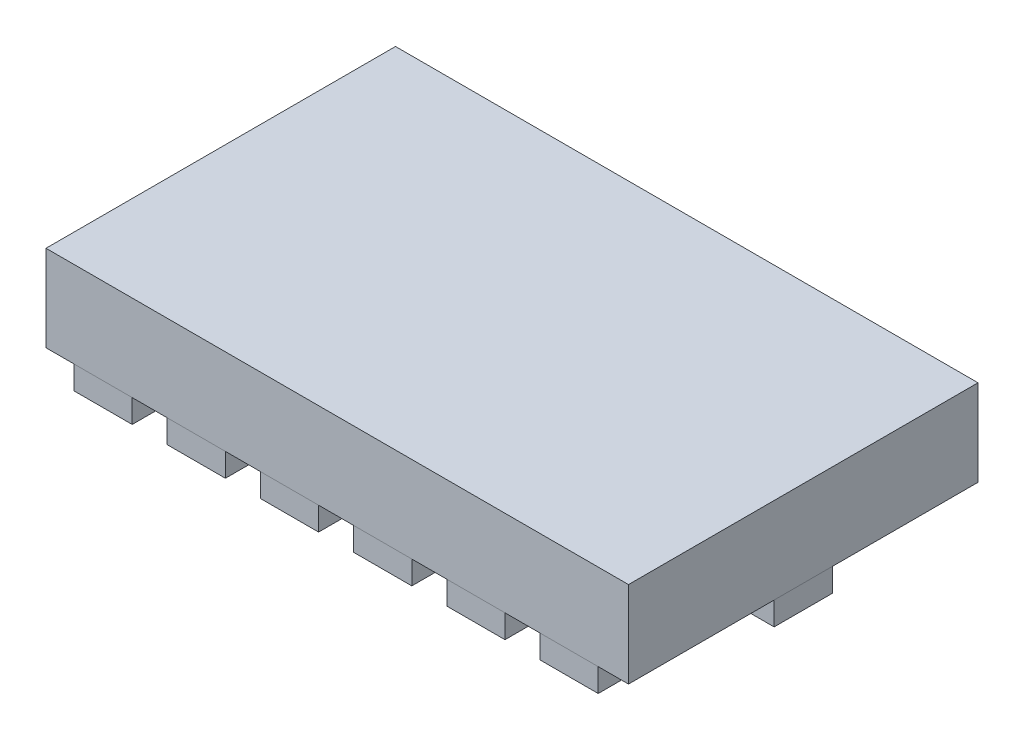
SolidWorks part; units mm, degrees
ref_plane "Front Plane" through (0, 0, 0) normal (0, 0, 1) x (1, 0, 0)
ref_plane "Top Plane" through (0, 0, 0) normal (0, 1, 0) x (1, 0, 0)
ref_plane "Right Plane" through (0, 0, 0) normal (1, 0, 0) x (0, 0, -1)
sketch "Sketch1" plane through (0, 0, 0) normal (0, 1, 0) x (1, 0, 0)
  line L1 (-2.5, -1.5) -> (2.5, -1.5)
  line L2 (-2.5, -1.5) -> (-2.5, 1.5)
  line L3 (-2.5, 1.5) -> (2.5, 1.5)
  line L4 (2.5, -1.5) -> (2.5, 1.5)
  line L5 (-2.5, -1.5) -> (2.5, 1.5) construction
  line L6 (-2.5, 1.5) -> (2.5, -1.5) construction
  point P0 (0, 0)
  dimension "D1" = 3
  dimension "D2" = 5
extrude "Boss-Extrude1" add sketch "Sketch1" along normal blind 0.74
sketch "Sketch2" plane through (0, 0, 0) normal (0, -1, 0) x (1, 0, 0)
  line L0 (-2.5, 0) -> (2.5, 0) construction
  line L1 (-2.5, -1.5) -> (-2.5, 1.5) construction
  line L2 (2.5, 1.5) -> (2.5, -1.5) construction
  line L3 (2.5, 0.25) -> (2.5, -0.25)
  line L4 (-2.5, 1.5) -> (2.5, 1.5) construction
  line L5 (0, 1.5) -> (0, -1.5) construction
  line L6 (2.5, -1.5) -> (-2.5, -1.5) construction
  line L7 (-2.5, 0.25) -> (-1.687, 0.25)
  line L8 (-2.5, 0.25) -> (-2.5, -0.25)
  line L9 (-2.5, -0.25) -> (-1.687, -0.25)
  line L10 (-1.687, 0.25) -> (-1.687, -0.25)
  line L11 (1.687, 0.25) -> (1.687, -0.25)
  line L12 (2.5, -0.25) -> (1.687, -0.25)
  line L13 (2.5, 0.25) -> (1.687, 0.25)
  line L14 (-2.01, 1.5) -> (-2.01, 0.687) construction
  line L15 (-2.26, 1.5) -> (-1.76, 1.5)
  line L16 (-2.26, 1.5) -> (-2.26, 0.687)
  line L17 (-2.26, 0.687) -> (-1.76, 0.687)
  line L18 (-1.76, 1.5) -> (-1.76, 0.687)
  line L19 (-1.46, 1.5) -> (-1.46, 0.687)
  line L20 (-1.46, 0.687) -> (-0.96, 0.687)
  line L21 (-0.96, 1.5) -> (-0.96, 0.687)
  line L22 (-1.46, 1.5) -> (-0.96, 1.5)
  line L23 (-0.66, 1.5) -> (-0.66, 0.687)
  line L24 (-0.66, 0.687) -> (-0.16, 0.687)
  line L25 (-0.16, 1.5) -> (-0.16, 0.687)
  line L26 (-0.66, 1.5) -> (-0.16, 1.5)
  line L27 (0.14, 1.5) -> (0.14, 0.687)
  line L28 (0.14, 0.687) -> (0.64, 0.687)
  line L29 (0.64, 1.5) -> (0.64, 0.687)
  line L30 (0.14, 1.5) -> (0.64, 1.5)
  line L31 (0.94, 1.5) -> (0.94, 0.687)
  line L32 (0.94, 0.687) -> (1.44, 0.687)
  line L33 (1.44, 1.5) -> (1.44, 0.687)
  line L34 (0.94, 1.5) -> (1.44, 1.5)
  line L35 (1.74, 1.5) -> (1.74, 0.687)
  line L36 (1.74, 0.687) -> (2.24, 0.687)
  line L37 (2.24, 1.5) -> (2.24, 0.687)
  line L38 (1.74, 1.5) -> (2.24, 1.5)
  line L39 (-2.26, 1.5) -> (-1.46, 1.5) construction
  line L40 (-2.26, -1.5) -> (-1.46, -1.5) construction
  line L41 (1.74, -1.5) -> (2.24, -1.5)
  line L42 (2.24, -1.5) -> (2.24, -0.687)
  line L43 (1.74, -0.687) -> (2.24, -0.687)
  line L44 (1.74, -1.5) -> (1.74, -0.687)
  line L45 (0.94, -1.5) -> (1.44, -1.5)
  line L46 (1.44, -1.5) -> (1.44, -0.687)
  line L47 (0.94, -0.687) -> (1.44, -0.687)
  line L48 (0.94, -1.5) -> (0.94, -0.687)
  line L49 (0.14, -1.5) -> (0.64, -1.5)
  line L50 (0.64, -1.5) -> (0.64, -0.687)
  line L51 (0.14, -0.687) -> (0.64, -0.687)
  line L52 (0.14, -1.5) -> (0.14, -0.687)
  line L53 (-0.66, -1.5) -> (-0.16, -1.5)
  line L54 (-0.16, -1.5) -> (-0.16, -0.687)
  line L55 (-0.66, -0.687) -> (-0.16, -0.687)
  line L56 (-0.66, -1.5) -> (-0.66, -0.687)
  line L57 (-1.46, -1.5) -> (-0.96, -1.5)
  line L58 (-0.96, -1.5) -> (-0.96, -0.687)
  line L59 (-1.46, -0.687) -> (-0.96, -0.687)
  line L60 (-1.46, -1.5) -> (-1.46, -0.687)
  line L61 (-1.76, -1.5) -> (-1.76, -0.687)
  line L62 (-2.26, -0.687) -> (-1.76, -0.687)
  line L63 (-2.26, -1.5) -> (-2.26, -0.687)
  line L64 (-2.26, -1.5) -> (-1.76, -1.5)
  dimension "D1" = 0.5
  dimension "D2" = 0.813
  dimension "D3" = 0.49
  dimension "D4" = 0.8
  dimension "D5" = 6
extrude "Boss-Extrude2" add sketch "Sketch2" along normal blind 0.2 separate body
